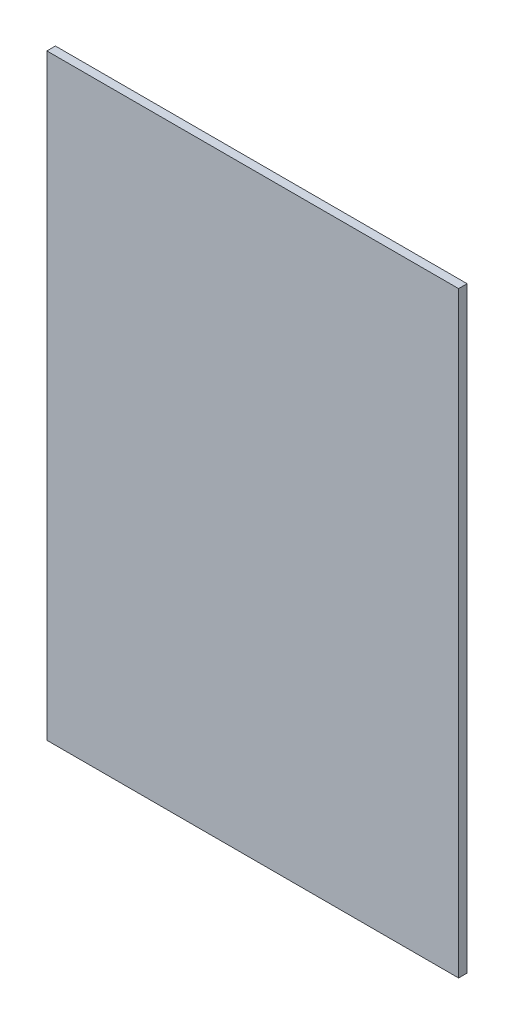
SolidWorks part; units mm, degrees
material "PMMA"
ref_plane "Front Plane" through (0, 0, 0) normal (0, 0, 1) x (1, 0, 0)
ref_plane "Top Plane" through (0, 0, 0) normal (0, 1, 0) x (1, 0, 0)
ref_plane "Right Plane" through (0, 0, 0) normal (1, 0, 0) x (0, 0, -1)
sketch "Sketch1" plane through (0, 0, 0) normal (0, 0, 1) x (1, 0, 0)
  line L1 (11551.2662, 9708.6163) -> (12518.399, 9708.6163)
  line L2 (11551.2662, 9708.6163) -> (11551.2662, 8306.0812)
  line L3 (11551.2662, 8306.0812) -> (12518.399, 8306.0812)
  line L4 (12518.399, 9708.6163) -> (12518.399, 8306.0812)
extrude "Boss-Extrude1" add sketch "Sketch1" along normal blind 20
